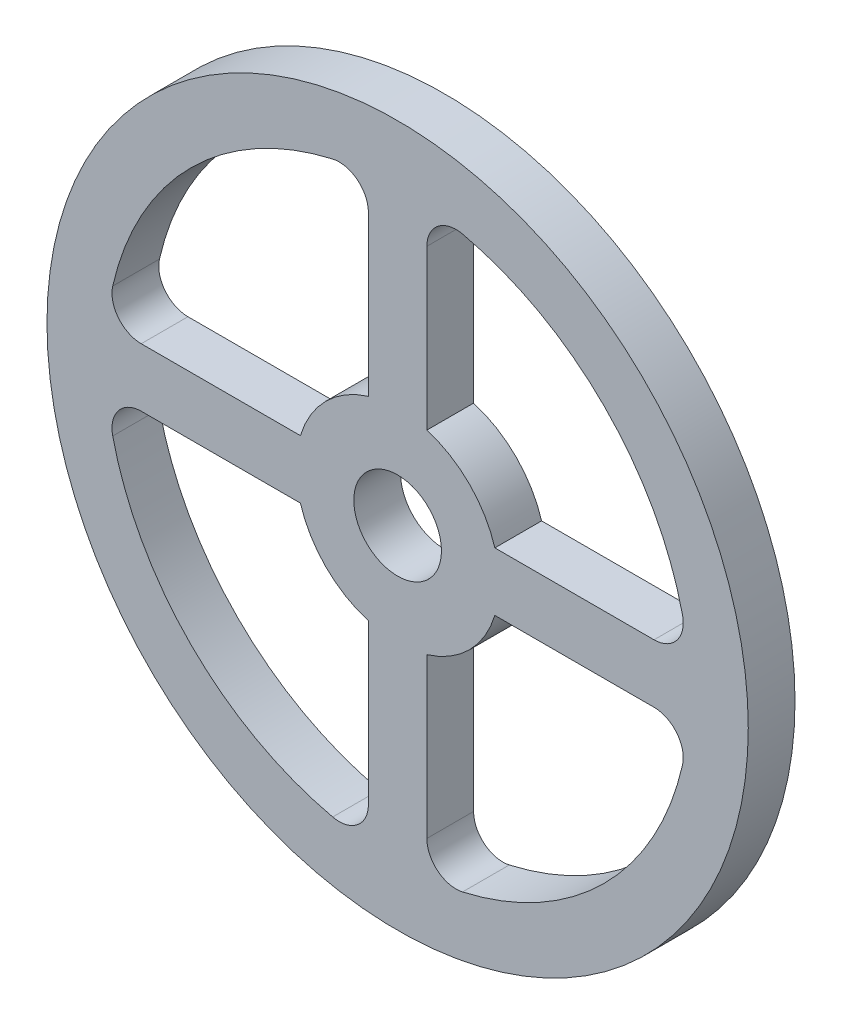
SolidWorks part; units mm, degrees
ref_plane "Front Plane" through (0, 0, 0) normal (0, 0, 1) x (1, 0, 0)
ref_plane "Top Plane" through (0, 0, 0) normal (0, 1, 0) x (1, 0, 0)
ref_plane "Right Plane" through (0, 0, 0) normal (1, 0, 0) x (0, 0, -1)
sketch "Sketch1" plane through (0, 0, 0) normal (0, 0, 1) x (1, 0, 0)
  line L0 (0, 164.355) -> (0, -195.8096) construction
  line L1 (181.5297, 0) -> (-234.4007, 0) construction
  line L3 (10, 87.7454) -> (10, 33.2682)
  line L4 (-10, 87.7454) -> (-10, 33.2682)
  line L5 (-10, -33.2682) -> (-10, -87.7454)
  line L6 (10, -33.2682) -> (10, -87.7454)
  line L9 (-87.7454, 10) -> (-33.2682, 10)
  line L11 (-87.7454, -10) -> (-33.2682, -10)
  line L12 (33.2682, 10) -> (87.7454, 10)
  line L13 (33.2682, -10) -> (87.7454, -10)
  circle A0 centre (0, 0) radius 120
  arc A2 (-22.2223, 97.4954) -> (-97.4954, 22.2223) centre (0, 0) ccw
  arc A3 (-33.2682, -10) -> (-10, -33.2682) centre (0, 0) ccw
  circle A4 centre (0, 0) radius 15
  arc A5 (10, -33.2682) -> (33.2682, -10) centre (0, 0) ccw
  arc A6 (-10, 33.2682) -> (-33.2682, 10) centre (0, 0) ccw
  arc A7 (33.2682, 10) -> (10, 33.2682) centre (0, 0) ccw
  arc A8 (-97.4954, -22.2223) -> (-22.2223, -97.4954) centre (0, 0) ccw
  arc A9 (97.4954, 22.2223) -> (22.2223, 97.4954) centre (0, 0) ccw
  arc A10 (22.2223, -97.4954) -> (97.4954, -22.2223) centre (0, 0) ccw
  arc A11 (87.7454, -10) -> (97.4954, -22.2223) centre (87.7454, -20) cw
  arc A12 (10, -87.7454) -> (22.2223, -97.4954) centre (20, -87.7454) ccw
  arc A13 (-10, -87.7454) -> (-22.2223, -97.4954) centre (-20, -87.7454) cw
  arc A14 (-87.7454, -10) -> (-97.4954, -22.2223) centre (-87.7454, -20) ccw
  arc A15 (-87.7454, 10) -> (-97.4954, 22.2223) centre (-87.7454, 20) cw
  arc A16 (-10, 87.7454) -> (-22.2223, 97.4954) centre (-20, 87.7454) ccw
  arc A17 (10, 87.7454) -> (22.2223, 97.4954) centre (20, 87.7454) cw
  arc A18 (87.7454, 10) -> (97.4954, 22.2223) centre (87.7454, 20) ccw
  point P6 (31.7045, 94.8411)
  point P11 (-34.7386, 0)
  point P28 (0, 0)
  point P29 (0, 0)
  dimension "D1" = 240
extrude "Boss-Extrude3" add sketch "Sketch1" along normal blind 16
